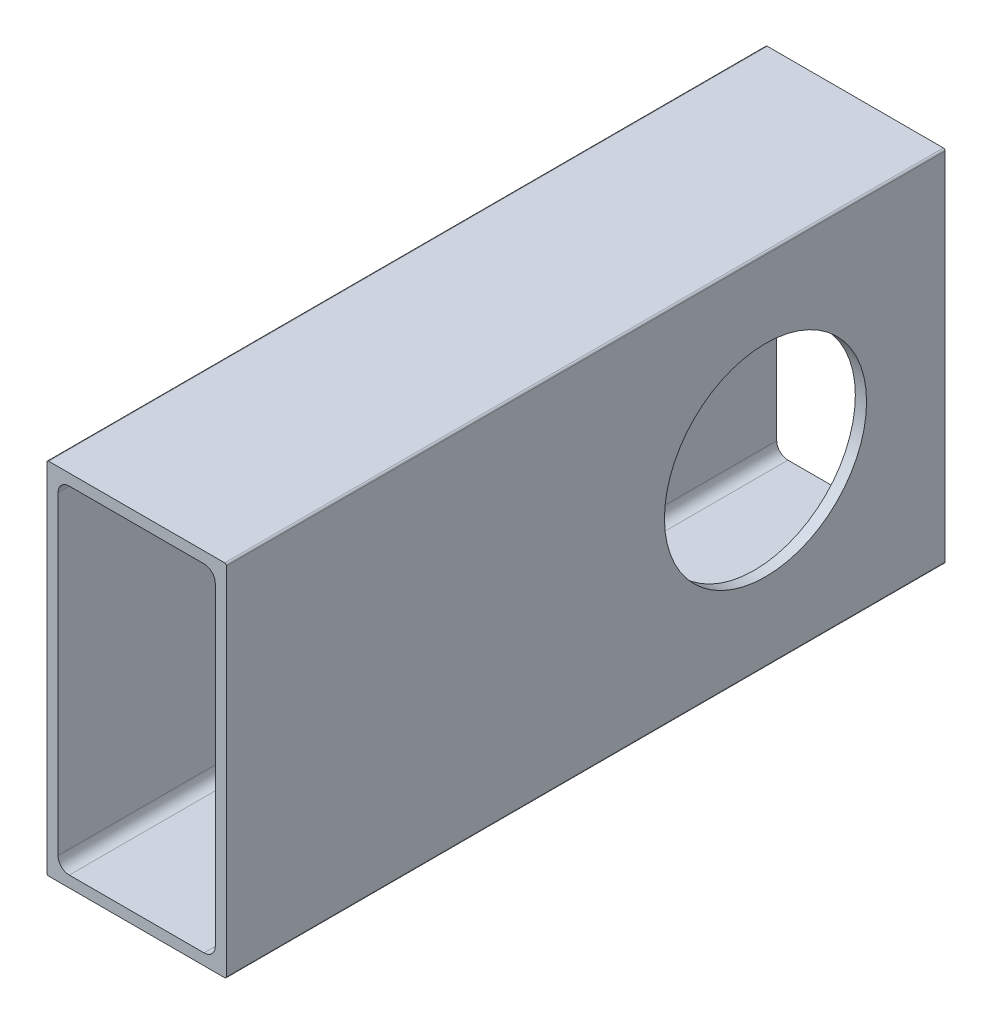
SolidWorks part; units mm, degrees
ref_plane "Front Plane" through (0, 0, 0) normal (0, 0, 1) x (1, 0, 0)
ref_plane "Top Plane" through (0, 0, 0) normal (0, 1, 0) x (1, 0, 0)
ref_plane "Right Plane" through (0, 0, 0) normal (1, 0, 0) x (0, 0, -1)
ref_plane "Plane1" through (0, 0, 0) normal (0, 0, -1) x (-1, 0, 0)
sketch "Sketch1" plane through (0, 0, 0) normal (0, 0, -1) x (-1, 0, 0)
  line L0 (-11.1125, -22.225) -> (-11.1125, 22.225)
  line L1 (-9.525, 23.8125) -> (9.525, 23.8125)
  line L2 (11.1125, 22.225) -> (11.1125, -22.225)
  line L3 (9.525, -23.8125) -> (-9.525, -23.8125)
  line L4 (-12.7, 25.146) -> (-12.7, -25.146)
  line L5 (-12.446, -25.4) -> (12.446, -25.4)
  line L6 (12.7, -25.146) -> (12.7, 25.146)
  line L7 (12.446, 25.4) -> (-12.446, 25.4)
  arc A0 (-11.1125, 22.225) -> (-9.525, 23.8125) centre (-9.525, 22.225) cw
  arc A1 (9.525, 23.8125) -> (11.1125, 22.225) centre (9.525, 22.225) cw
  arc A2 (11.1125, -22.225) -> (9.525, -23.8125) centre (9.525, -22.225) cw
  arc A3 (-9.525, -23.8125) -> (-11.1125, -22.225) centre (-9.525, -22.225) cw
  arc A4 (-12.7, -25.146) -> (-12.446, -25.4) centre (-12.446, -25.146) ccw
  arc A5 (12.446, -25.4) -> (12.7, -25.146) centre (12.446, -25.146) ccw
  arc A6 (12.7, 25.146) -> (12.446, 25.4) centre (12.446, 25.146) ccw
  arc A7 (-12.446, 25.4) -> (-12.7, 25.146) centre (-12.446, 25.146) ccw
extrude "Boss-Extrude1" add sketch "Sketch1" against normal blind 101.6
sketch "Sketch2" plane through (-12.7, 0, 0) normal (-1, 0, 0) x (0, 0, 1)
  line L0 (0, 0) -> (25.4, 0) construction
  circle A0 centre (25.4, 0) radius 14.2875
  dimension "D1" = 28.575
  dimension "D2" = 25.4
extrude "Cut-Extrude1" cut sketch "Sketch2" against normal blind 50.8
